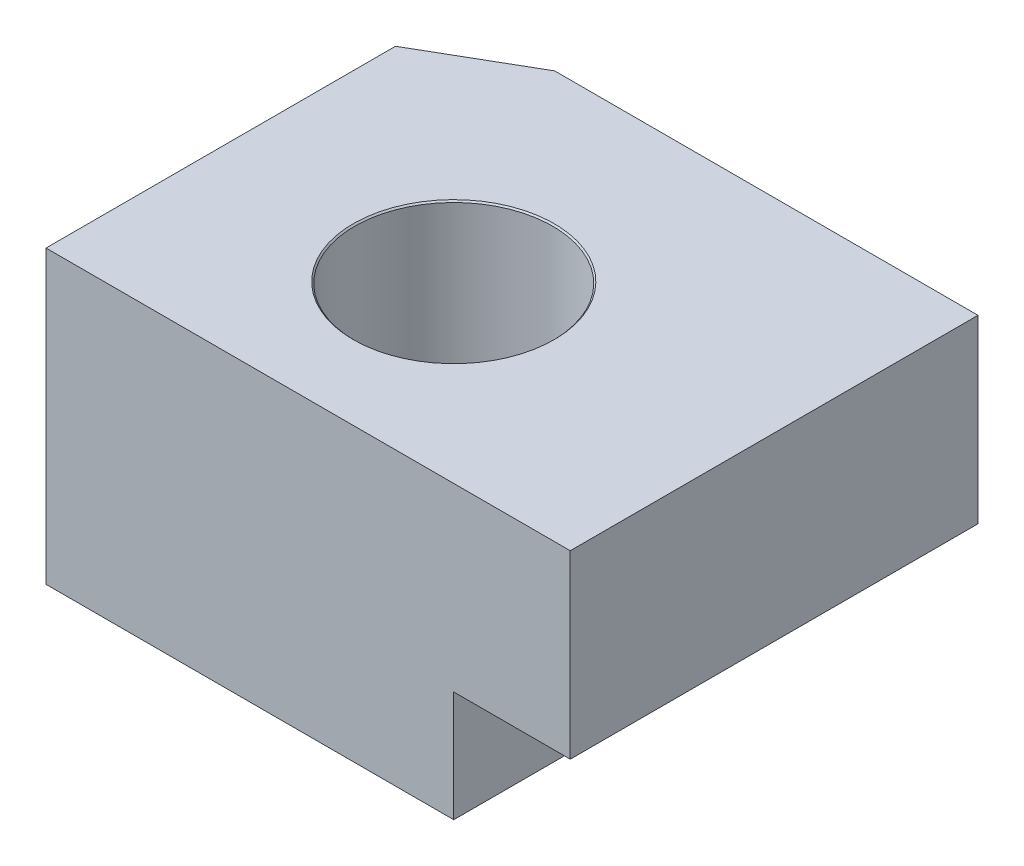
SolidWorks part; units mm, degrees
material "2024 Сплав"
ref_plane "Спереди" through (0, 0, 0) normal (0, 0, 1) x (1, 0, 0)
ref_plane "Сверху" through (0, 0, 0) normal (0, 1, 0) x (1, 0, 0)
ref_plane "Справа" through (0, 0, 0) normal (1, 0, 0) x (0, 0, -1)
sketch "Эскиз1" plane through (0, 0, 0) normal (0, 0, 1) x (1, 0, 0)
  line L0 (0, 0) -> (0, 1.9)
  line L1 (0, 1.9) -> (2, 1.9)
  line L2 (2, 1.9) -> (2, 5)
  line L3 (2, 5) -> (-7, 5)
  line L4 (-7, 5) -> (-7, 0)
  line L5 (-7, 0) -> (0, 0)
  dimension "D1" = 7
  dimension "D2" = 5
  dimension "D3" = 1.9
  dimension "D4" = 9
extrude "Бобышка-Вытянуть1" add sketch "Эскиз1" along normal blind 7
hole_wizard "Отверстие с зазором M31" positions "Эскиз3" profile "Эскиз4" hole size "M3" standard "Ansi (метрические)" end condition through all
sketch "Эскиз3" plane through (0, 5, 0) normal (0, 1, 0) x (-1, 0, 0)
  line L0 (-2, 7) -> (7, 7) construction
  line L1 (0, 7) -> (0, 0) construction
  point P0 (3, 4)
  dimension "D1" = 3
  dimension "D2" = 3
sketch "Эскиз4" plane through (-3, 5, 4) normal (1, 0, 0) x (0, 0, 1)
  line L0 (0, 0) -> (0, 5)
  line L1 (0, 5) -> (1.725, 5)
  line L2 (1.7, 4.975) -> (1.7, 0.025)
  line L3 (1.7, 0.025) -> (1.725, 0)
  line L5 (1.725, 0) -> (0, 0)
  line L6 (-1.7, 0.025) -> (-1.725, 0) construction
  line L7 (1.725, 5) -> (1.7, 4.975)
  line L8 (-1.725, 5) -> (-1.7, 4.975) construction
  line L11 (0, -6.35) -> (0, 107.95) construction
  dimension "Диаметр сквозного отверстия" = 3.4
  dimension "Глубина сквозного отверстия" = 5
  dimension "Диаметр передней зенковки" = 3.45
  dimension "Угол передней зенковки" = 90
  dimension "Диаметр задней зенковки" = 3.45
  dimension "Угол задней зенковки" = 90
chamfer "Фаска1" distance 1 angle 60 1 edges at (-7, 2.5, 0)
